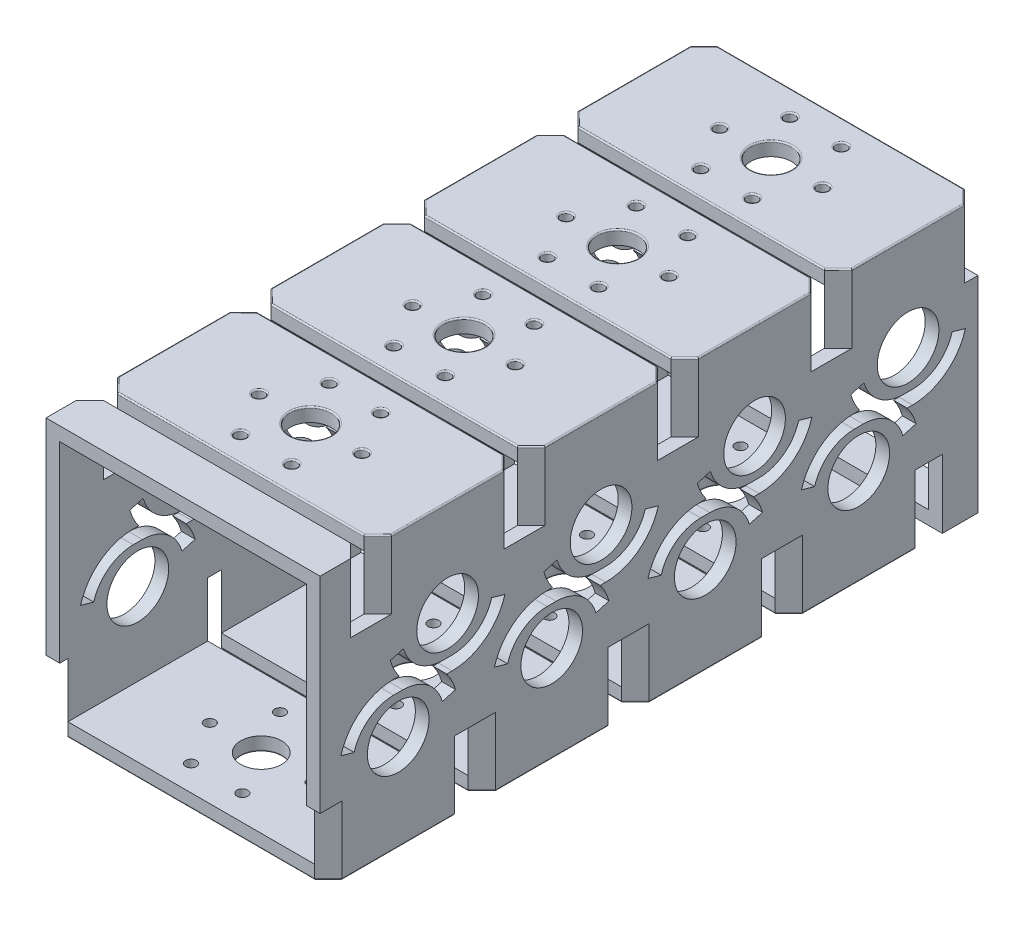
SolidWorks part; units mm, degrees
ref_plane "Front" through (0, 0, 0) normal (0, 0, 1) x (1, 0, 0)
ref_plane "Top" through (0, 0, 0) normal (0, 1, 0) x (1, 0, 0)
ref_plane "Right" through (0, 0, 0) normal (1, 0, 0) x (0, 0, -1)
sketch "Sketch1" plane through (0, 0, 0) normal (0, 0, 1) x (1, 0, 0)
  line L0 (6.35, 6.35) -> (120.65, 6.35)
  line L1 (0, 0) -> (127, 0)
  line L2 (0, 0) -> (0, 127)
  line L3 (0, 127) -> (127, 127)
  line L4 (127, 0) -> (127, 127)
  line L5 (120.65, 6.35) -> (120.65, 120.65)
  line L6 (6.35, 120.65) -> (120.65, 120.65)
  line L7 (6.35, 6.35) -> (6.35, 120.65)
  dimension "D1" = 127
  dimension "D2" = 6.35
extrude "Boss-Extrude1" add sketch "Sketch1" along normal blind 304.8
sketch "Sketch2" plane through (0, 127, 0) normal (0, 1, 0) x (1, 0, 0)
  line L0 (6.35, -64.77) -> (0, -64.77) construction
  line L1 (0, -304.8) -> (0, 0) construction
  line L2 (120.65, -71.12) -> (127, -71.12) construction
  line L3 (127, -304.8) -> (127, 0) construction
  line L5 (0, -64.77) -> (127, -64.77)
  line L6 (0, -64.77) -> (0, -71.12)
  line L7 (0, -71.12) -> (127, -71.12)
  line L8 (127, -64.77) -> (127, -71.12)
  line L9 (0, -64.77) -> (127, -71.12) construction
  line L10 (0, -71.12) -> (127, -64.77) construction
  point P13 (63.5, -67.945)
extrude "Cut-Extrude1" cut sketch "Sketch2" against normal blind 31.75
sketch "Sketch3" plane through (0, 127, 0) normal (0, 1, 0) x (1, 0, 0)
  line L0 (0, -58.42) -> (6.35, -64.77) construction
  line L1 (0, -58.42) -> (6.35, -64.77)
  line L2 (6.35, -64.77) -> (0, -64.77)
  line L4 (0, -64.77) -> (0, -58.42)
  line L5 (6.35, -71.12) -> (0, -77.47) construction
  line L6 (6.35, -71.12) -> (0, -77.47)
  line L7 (6.35, -71.12) -> (0, -71.12)
  line L8 (0, -71.12) -> (0, -77.47)
extrude "Cut-Extrude2" cut sketch "Sketch3" against normal blind 31.75
sketch "Sketch5" plane through (0, 0, 0) normal (-1, 0, 0) x (0, 0, 1)
  circle A0 centre (55.245, 44.45) radius 14.2875
  circle A1 centre (32.385, 82.55) radius 14.2875
  circle A2 centre (103.505, 82.55) radius 14.2875
  circle A3 centre (174.625, 82.55) radius 14.2875
  circle A4 centre (245.745, 82.55) radius 14.2875
  circle A9 centre (126.365, 44.45) radius 14.2875
  circle A10 centre (197.485, 44.45) radius 14.2875
  circle A11 centre (268.605, 44.45) radius 14.2875
  dimension "D1" = 28.575
  dimension "D4" = 4
  dimension "D2" = 4
  dimension "D3" = 1
extrude "Cut-Extrude4" cut sketch "Sketch5" against normal through all
pattern_linear "LPattern2" count 4 spacing 71.12 along (0, 0, 1) of "Cut-Extrude1"
pattern_linear "LPattern3" count 4 spacing 71.12 along (0, 0, 1) of "Cut-Extrude2"
sketch "Sketch6" plane through (0, 127, 0) normal (0, 1, 0) x (1, 0, 0)
  line L0 (6.35, 0) -> (0, -6.35) construction
  line L1 (6.35, 0) -> (0, -6.35)
  line L2 (6.35, 0) -> (0, 0)
  line L3 (0, 0) -> (0, -6.35)
  line L4 (127, -6.35) -> (120.65, 0) construction
  line L5 (127, -6.35) -> (120.65, 0)
  line L6 (127, -6.35) -> (127, 0)
  line L7 (127, 0) -> (120.65, 0)
extrude "Cut-Extrude5" cut sketch "Sketch6" against normal blind 31.75
sketch "Sketch7" plane through (0, 127, 0) normal (0, 1, 0) x (1, 0, 0)
  line L0 (127, -77.47) -> (120.65, -71.12) construction
  line L1 (127, -77.47) -> (120.65, -71.12)
  line L2 (120.65, -64.77) -> (127, -58.42) construction
  line L3 (120.65, -64.77) -> (127, -58.42)
  line L4 (120.65, -71.12) -> (127, -71.12)
  line L5 (127, -71.12) -> (127, -77.47)
  line L6 (120.65, -64.77) -> (127, -64.77)
  line L7 (127, -64.77) -> (127, -58.42)
extrude "Cut-Extrude6" cut sketch "Sketch7" against normal blind 31.75
pattern_linear "LPattern4" count 4 spacing 71.12 along (0, 0, 1) of "Cut-Extrude6"
sketch "Sketch8" plane through (0, 127, 0) normal (0, 1, 0) x (1, 0, 0)
  circle A1 centre (87.3125, -32.385) radius 2.4892
  circle A3 centre (75.4062, -53.0072) radius 2.4892
  circle A4 centre (51.5937, -53.0072) radius 2.4892
  circle A5 centre (39.6875, -32.385) radius 2.4892
  circle A6 centre (51.5938, -11.7628) radius 2.4892
  circle A7 centre (75.4063, -11.7628) radius 2.4892
  circle A9 centre (63.5, -32.385) radius 9.4869
  point P18 (63.5, -32.385)
  dimension "D1" = 18.9738
  dimension "D2" = 4.9784
  dimension "D3" = 6
extrude "Cut-Extrude7" cut sketch "Sketch8" against normal up to next (6.35 mm away)
pattern_linear "LPattern5" count 4 spacing 71.12 along (0, 0, 1) of "Cut-Extrude7"
ref_plane "Plane1" through (0, 63.5, 0) normal (0, 1, 0) x (1, 0, 0)
sketch "Sketch9" plane through (0, 0, 0) normal (0, -1, 0) x (1, 0, 0)
  circle A0 centre (51.5937, 34.6228) radius 2.4892
  circle A1 centre (39.6875, 55.245) radius 2.4892
  circle A2 centre (51.5937, 75.8672) radius 2.4892
  circle A3 centre (75.4062, 75.8672) radius 2.4892
  circle A4 centre (87.3125, 55.245) radius 2.4892
  circle A5 centre (75.4062, 34.6228) radius 2.4892
  circle A6 centre (63.5, 55.245) radius 9.4869
  circle A7 centre (51.5937, 105.7428) radius 2.4892
  circle A8 centre (39.6875, 126.365) radius 2.4892
  circle A9 centre (51.5937, 146.9872) radius 2.4892
  circle A10 centre (75.4062, 146.9872) radius 2.4892
  circle A11 centre (87.3125, 126.365) radius 2.4892
  circle A12 centre (75.4062, 105.7428) radius 2.4892
  circle A13 centre (63.5, 126.365) radius 9.4869
  circle A14 centre (51.5937, 176.8628) radius 2.4892
  circle A15 centre (39.6875, 197.485) radius 2.4892
  circle A16 centre (51.5937, 218.1072) radius 2.4892
  circle A17 centre (75.4062, 218.1072) radius 2.4892
  circle A18 centre (87.3125, 197.485) radius 2.4892
  circle A19 centre (75.4062, 176.8628) radius 2.4892
  circle A20 centre (63.5, 197.485) radius 9.4869
  circle A21 centre (51.5937, 247.9828) radius 2.4892
  circle A22 centre (39.6875, 268.605) radius 2.4892
  circle A23 centre (51.5937, 289.2272) radius 2.4892
  circle A24 centre (75.4062, 289.2272) radius 2.4892
  circle A25 centre (87.3125, 268.605) radius 2.4892
  circle A26 centre (75.4062, 247.9828) radius 2.4892
  circle A27 centre (63.5, 268.605) radius 9.4869
  dimension "D1" = 4.9784
  dimension "D2" = 18.9738
  dimension "D3" = 4
extrude "Cut-Extrude8" cut sketch "Sketch9" against normal up to next (6.35 mm away)
sketch "Sketch10" plane through (0, 0, 0) normal (0, -1, 0) x (1, 0, 0)
  line L0 (127, 304.8) -> (127, 0) construction
  line L1 (127, 22.86) -> (0, 22.86)
  line L2 (127, 22.86) -> (127, 16.51)
  line L3 (127, 16.51) -> (0, 16.51)
  line L4 (0, 22.86) -> (0, 16.51)
  line L5 (127, 22.86) -> (0, 16.51) construction
  line L6 (127, 16.51) -> (0, 22.86) construction
  line L7 (0, 304.8) -> (0, 0) construction
  line L8 (6.35, 22.86) -> (120.65, 22.86) construction
  line L9 (127, 93.98) -> (0, 93.98)
  line L10 (127, 93.98) -> (127, 87.63)
  line L11 (127, 87.63) -> (0, 87.63)
  line L12 (0, 93.98) -> (0, 87.63)
  line L13 (127, 93.98) -> (0, 87.63) construction
  line L14 (127, 87.63) -> (0, 93.98) construction
  line L15 (127, 165.1) -> (0, 165.1)
  line L16 (127, 165.1) -> (127, 158.75)
  line L17 (127, 158.75) -> (0, 158.75)
  line L18 (0, 165.1) -> (0, 158.75)
  line L19 (127, 165.1) -> (0, 158.75) construction
  line L20 (127, 158.75) -> (0, 165.1) construction
  line L21 (127, 236.22) -> (0, 236.22)
  line L22 (127, 236.22) -> (127, 229.87)
  line L23 (127, 229.87) -> (0, 229.87)
  line L24 (0, 236.22) -> (0, 229.87)
  line L25 (127, 236.22) -> (0, 229.87) construction
  line L26 (127, 229.87) -> (0, 236.22) construction
  line L27 (127, 307.34) -> (0, 307.34)
  line L28 (127, 307.34) -> (127, 300.99)
  line L29 (127, 300.99) -> (0, 300.99)
  line L30 (0, 307.34) -> (0, 300.99)
  line L31 (127, 307.34) -> (0, 300.99) construction
  line L32 (127, 300.99) -> (0, 307.34) construction
  point P4 (63.5, 19.685)
  point P16 (63.5, 90.805)
  point P21 (63.5, 161.925)
  point P26 (63.5, 233.045)
  point P31 (63.5, 304.165)
  dimension "D1" = 6.35
  dimension "D2" = 5
extrude "Cut-Extrude9" cut sketch "Sketch10" against normal blind 31.75
sketch "Sketch11" plane through (0, 0, 0) normal (0, -1, 0) x (1, 0, 0)
  line L0 (120.65, 22.86) -> (127, 29.21) construction
  line L1 (127, 81.28) -> (120.65, 87.63) construction
  line L2 (6.35, 87.63) -> (0, 81.28) construction
  line L3 (0, 29.21) -> (6.35, 22.86) construction
  line L4 (120.65, 22.86) -> (127, 29.21)
  line L5 (127, 81.28) -> (120.65, 87.63)
  line L6 (6.35, 87.63) -> (0, 81.28)
  line L7 (0, 29.21) -> (6.35, 22.86)
  line L8 (6.35, 22.86) -> (0, 22.86)
  line L9 (0, 22.86) -> (0, 29.21)
  line L10 (0, 81.28) -> (0, 87.63)
  line L11 (0, 87.63) -> (6.35, 87.63)
  line L12 (120.65, 22.86) -> (127, 22.86)
  line L13 (127, 22.86) -> (127, 29.21)
  line L14 (127, 81.28) -> (127, 87.63)
  line L15 (127, 87.63) -> (120.65, 87.63)
  line L16 (120.65, 93.98) -> (127, 100.33)
  line L17 (127, 152.4) -> (120.65, 158.75)
  line L18 (6.35, 158.75) -> (0, 152.4)
  line L19 (0, 100.33) -> (6.35, 93.98)
  line L20 (6.35, 93.98) -> (0, 93.98)
  line L21 (0, 93.98) -> (0, 100.33)
  line L22 (0, 152.4) -> (0, 158.75)
  line L23 (0, 158.75) -> (6.35, 158.75)
  line L24 (120.65, 93.98) -> (127, 93.98)
  line L25 (127, 93.98) -> (127, 100.33)
  line L26 (127, 152.4) -> (127, 158.75)
  line L27 (127, 158.75) -> (120.65, 158.75)
  line L28 (120.65, 165.1) -> (127, 171.45)
  line L29 (127, 223.52) -> (120.65, 229.87)
  line L30 (6.35, 229.87) -> (0, 223.52)
  line L31 (0, 171.45) -> (6.35, 165.1)
  line L32 (6.35, 165.1) -> (0, 165.1)
  line L33 (0, 165.1) -> (0, 171.45)
  line L34 (0, 223.52) -> (0, 229.87)
  line L35 (0, 229.87) -> (6.35, 229.87)
  line L36 (120.65, 165.1) -> (127, 165.1)
  line L37 (127, 165.1) -> (127, 171.45)
  line L38 (127, 223.52) -> (127, 229.87)
  line L39 (127, 229.87) -> (120.65, 229.87)
  line L40 (120.65, 236.22) -> (127, 242.57)
  line L41 (127, 294.64) -> (120.65, 300.99)
  line L42 (6.35, 300.99) -> (0, 294.64)
  line L43 (0, 242.57) -> (6.35, 236.22)
  line L44 (6.35, 236.22) -> (0, 236.22)
  line L45 (0, 236.22) -> (0, 242.57)
  line L46 (0, 294.64) -> (0, 300.99)
  line L47 (0, 300.99) -> (6.35, 300.99)
  line L48 (120.65, 236.22) -> (127, 236.22)
  line L49 (127, 236.22) -> (127, 242.57)
  line L50 (127, 294.64) -> (127, 300.99)
  line L51 (127, 300.99) -> (120.65, 300.99)
  dimension "D1" = 4
extrude "Cut-Extrude10" cut sketch "Sketch11" against normal blind 31.75
sketch "Sketch12" plane through (127, 0, 0) normal (1, 0, 0) x (0, 0, -1)
  line L0 (-53.1269, 62.23) -> (-57.3631, 62.23) construction
  line L1 (-53.1269, 62.23) -> (-57.3631, 62.23)
  line L3 (-34.802, 48.3859) -> (-28.6937, 50.1212)
  line L4 (-53.1269, 68.58) -> (-57.3631, 68.58)
  line L5 (-53.1269, 68.58) -> (-57.3631, 68.58)
  line L6 (-75.688, 48.3859) -> (-81.7963, 50.1212)
  line L7 (-146.808, 48.3859) -> (-152.9163, 50.1212)
  line L8 (-124.2469, 68.58) -> (-128.4831, 68.58)
  line L9 (-124.2469, 62.23) -> (-128.4831, 62.23)
  line L10 (-105.922, 48.3859) -> (-99.8137, 50.1212)
  line L11 (-217.928, 48.3859) -> (-224.0363, 50.1212)
  line L12 (-195.3669, 68.58) -> (-199.6031, 68.58)
  line L13 (-195.3669, 62.23) -> (-199.6031, 62.23)
  line L14 (-177.042, 48.3859) -> (-170.9337, 50.1212)
  line L15 (-289.048, 48.3859) -> (-295.1563, 50.1212)
  line L16 (-266.4869, 68.58) -> (-270.7231, 68.58)
  line L17 (-266.4869, 62.23) -> (-270.7231, 62.23)
  line L18 (-248.162, 48.3859) -> (-242.0537, 50.1212)
  arc A0 (-57.3631, 62.23) -> (-75.688, 48.3859) centre (-57.3631, 43.18) ccw construction
  arc A1 (-34.802, 48.3859) -> (-53.1269, 62.23) centre (-53.1269, 43.18) ccw construction
  arc A2 (-57.3631, 62.23) -> (-75.688, 48.3859) centre (-57.3631, 43.18) ccw
  arc A3 (-34.802, 48.3859) -> (-53.1269, 62.23) centre (-53.1269, 43.18) ccw
  arc A6 (-128.4831, 62.23) -> (-146.808, 48.3859) centre (-128.4831, 43.18) ccw
  arc A7 (-128.4831, 68.58) -> (-152.9163, 50.1212) centre (-128.4831, 43.18) ccw
  arc A8 (-28.6937, 50.1212) -> (-53.1269, 68.58) centre (-53.1269, 43.18) ccw
  arc A9 (-57.3631, 68.58) -> (-81.7963, 50.1212) centre (-57.3631, 43.18) ccw
  arc A10 (-28.6937, 50.1212) -> (-53.1269, 68.58) centre (-53.1269, 43.18) ccw
  arc A11 (-57.3631, 68.58) -> (-81.7963, 50.1212) centre (-57.3631, 43.18) ccw
  arc A12 (-99.8137, 50.1212) -> (-124.2469, 68.58) centre (-124.2469, 43.18) ccw
  arc A13 (-105.922, 48.3859) -> (-124.2469, 62.23) centre (-124.2469, 43.18) ccw
  arc A14 (-199.6031, 62.23) -> (-217.928, 48.3859) centre (-199.6031, 43.18) ccw
  arc A15 (-199.6031, 68.58) -> (-224.0363, 50.1212) centre (-199.6031, 43.18) ccw
  arc A16 (-170.9337, 50.1212) -> (-195.3669, 68.58) centre (-195.3669, 43.18) ccw
  arc A17 (-177.042, 48.3859) -> (-195.3669, 62.23) centre (-195.3669, 43.18) ccw
  arc A18 (-270.7231, 62.23) -> (-289.048, 48.3859) centre (-270.7231, 43.18) ccw
  arc A19 (-270.7231, 68.58) -> (-295.1563, 50.1212) centre (-270.7231, 43.18) ccw
  arc A20 (-242.0537, 50.1212) -> (-266.4869, 68.58) centre (-266.4869, 43.18) ccw
  arc A21 (-248.162, 48.3859) -> (-266.4869, 62.23) centre (-266.4869, 43.18) ccw
  dimension "D2" = 4
  dimension "D1" = 6.35
extrude "Cut-Extrude11" cut sketch "Sketch12" against normal through all
sketch "Sketch13" plane through (127, 0, 0) normal (1, 0, 0) x (0, 0, -1)
  line L0 (-34.5031, 64.77) -> (-30.2669, 64.77) construction
  line L1 (-34.5031, 64.77) -> (-30.2669, 64.77)
  line L3 (-52.828, 78.6141) -> (-58.9363, 76.8788)
  line L4 (-34.5031, 58.42) -> (-30.2669, 58.42)
  line L5 (-34.5031, 58.42) -> (-30.2669, 58.42)
  line L6 (-11.942, 78.6141) -> (-5.8337, 76.8788)
  line L7 (-123.948, 78.6141) -> (-130.0563, 76.8788)
  line L8 (-105.6231, 64.77) -> (-101.3869, 64.77)
  line L9 (-105.6231, 58.42) -> (-101.3869, 58.42)
  line L10 (-83.062, 78.6141) -> (-76.9537, 76.8788)
  line L11 (-195.068, 78.6141) -> (-201.1763, 76.8788)
  line L12 (-176.7431, 64.77) -> (-172.5069, 64.77)
  line L13 (-176.7431, 58.42) -> (-172.5069, 58.42)
  line L14 (-154.182, 78.6141) -> (-148.0737, 76.8788)
  line L15 (-266.188, 78.6141) -> (-272.2963, 76.8788)
  line L16 (-247.8631, 64.77) -> (-243.6269, 64.77)
  line L17 (-247.8631, 58.42) -> (-243.6269, 58.42)
  line L18 (-225.302, 78.6141) -> (-219.1937, 76.8788)
  arc A0 (-52.828, 78.6141) -> (-34.5031, 64.77) centre (-34.5031, 83.82) ccw construction
  arc A1 (-30.2669, 64.77) -> (-11.942, 78.6141) centre (-30.2669, 83.82) ccw construction
  arc A2 (-52.828, 78.6141) -> (-34.5031, 64.77) centre (-34.5031, 83.82) ccw
  arc A3 (-30.2669, 64.77) -> (-11.942, 78.6141) centre (-30.2669, 83.82) ccw
  arc A6 (-130.0563, 76.8788) -> (-105.6231, 58.42) centre (-105.6231, 83.82) ccw
  arc A7 (-123.948, 78.6141) -> (-105.6231, 64.77) centre (-105.6231, 83.82) ccw
  arc A8 (-30.2669, 58.42) -> (-5.8337, 76.8788) centre (-30.2669, 83.82) ccw
  arc A9 (-58.9363, 76.8788) -> (-34.5031, 58.42) centre (-34.5031, 83.82) ccw
  arc A10 (-30.2669, 58.42) -> (-5.8337, 76.8788) centre (-30.2669, 83.82) ccw
  arc A11 (-58.9363, 76.8788) -> (-34.5031, 58.42) centre (-34.5031, 83.82) ccw
  arc A12 (-101.3869, 58.42) -> (-76.9537, 76.8788) centre (-101.3869, 83.82) ccw
  arc A13 (-101.3869, 64.77) -> (-83.062, 78.6141) centre (-101.3869, 83.82) ccw
  arc A14 (-201.1763, 76.8788) -> (-176.7431, 58.42) centre (-176.7431, 83.82) ccw
  arc A15 (-195.068, 78.6141) -> (-176.7431, 64.77) centre (-176.7431, 83.82) ccw
  arc A16 (-172.5069, 58.42) -> (-148.0737, 76.8788) centre (-172.5069, 83.82) ccw
  arc A17 (-172.5069, 64.77) -> (-154.182, 78.6141) centre (-172.5069, 83.82) ccw
  arc A18 (-272.2963, 76.8788) -> (-247.8631, 58.42) centre (-247.8631, 83.82) ccw
  arc A19 (-266.188, 78.6141) -> (-247.8631, 64.77) centre (-247.8631, 83.82) ccw
  arc A20 (-243.6269, 58.42) -> (-219.1937, 76.8788) centre (-243.6269, 83.82) ccw
  arc A21 (-243.6269, 64.77) -> (-225.302, 78.6141) centre (-243.6269, 83.82) ccw
  dimension "D2" = 4
  dimension "D1" = 6.35
extrude "Cut-Extrude12" cut sketch "Sketch13" against normal through all
fillet "Fillet1" radius 0.635 120 edges at (123.825, 127, 274.955) (63.5, 127, 278.13) (3.175, 127, 274.955) (0, 127, 245.745) (3.175, 127, 216.535) (63.5, 127, 213.36) (123.825, 127, 216.535) (127, 127, 245.745) (75.4063, 127, 227.612) (51.5938, 127, 227.612) (39.6875, 127, 248.2342) (51.5937, 127, 268.8564) (87.3125, 127, 248.2342) (63.5, 127, 255.2319) (75.4062, 127, 268.8564) (3.175, 127, 203.835) (0, 127, 174.625) (3.175, 127, 145.415) (63.5, 127, 142.24) (123.825, 127, 145.415) (127, 127, 174.625) (123.825, 127, 203.835) (63.5, 127, 207.01) (63.5, 127, 184.1119) (87.3125, 127, 177.1142) (75.4063, 127, 156.492) (51.5938, 127, 156.492) (39.6875, 127, 177.1142) (51.5937, 127, 197.7364) (75.4062, 127, 197.7364) (3.175, 127, 132.715) (0, 127, 103.505) (3.175, 127, 74.295) (63.5, 127, 71.12) (123.825, 127, 74.295) (127, 127, 103.505) (123.825, 127, 132.715) (63.5, 127, 135.89) (87.3125, 127, 105.9942) (75.4063, 127, 85.372) (51.5938, 127, 85.372) (63.5, 127, 112.9919) (75.4062, 127, 126.6164) (51.5937, 127, 126.6164) (39.6875, 127, 105.9942) (3.175, 127, 61.595) (0, 127, 32.385) (3.175, 127, 3.175) (63.5, 127, 0) (123.825, 127, 3.175) (127, 127, 32.385) (123.825, 127, 61.595) (63.5, 127, 64.77) (75.4063, 127, 14.252) (51.5938, 127, 14.252) (63.5, 127, 41.8719) (75.4062, 127, 55.4964) (51.5937, 127, 55.4964) (39.6875, 127, 34.8742) (87.3125, 127, 34.8742) (123.825, 0, 26.035) (63.5, 0, 22.86) (3.175, 0, 26.035) (0, 0, 55.245) (3.175, 0, 84.455) (63.5, 0, 87.63) (123.825, 0, 84.455) (127, 0, 55.245) (39.6875, 0, 52.7558) (51.5937, 0, 73.378) (75.4062, 0, 73.378) (87.3125, 0, 52.7558) (75.4062, 0, 32.1336) (63.5, 0, 45.7581) (51.5937, 0, 32.1336) (123.825, 0, 97.155) (63.5, 0, 93.98) (3.175, 0, 97.155) (0, 0, 126.365) (3.175, 0, 155.575) (63.5, 0, 158.75) (123.825, 0, 155.575) (127, 0, 126.365) (39.6875, 0, 123.8758) (51.5937, 0, 103.2536) (63.5, 0, 116.8781) (75.4062, 0, 103.2536) (87.3125, 0, 123.8758) (75.4062, 0, 144.498) (51.5937, 0, 144.498) (3.175, 0, 168.275) (0, 0, 197.485) (3.175, 0, 226.695) (63.5, 0, 229.87) (123.825, 0, 226.695) (127, 0, 197.485) (123.825, 0, 168.275) (63.5, 0, 165.1) (51.5937, 0, 174.3736) (39.6875, 0, 194.9958) (51.5937, 0, 215.618) (75.4062, 0, 215.618) (87.3125, 0, 194.9958) (75.4062, 0, 174.3736) (63.5, 0, 187.9981) (3.175, 0, 297.815) (63.5, 0, 300.99) (123.825, 0, 297.815) (127, 0, 268.605) (123.825, 0, 239.395) (63.5, 0, 236.22) (3.175, 0, 239.395) (0, 0, 268.605) (51.5937, 0, 245.4936) (39.6875, 0, 266.1158) (51.5937, 0, 286.738) (75.4062, 0, 286.738) (63.5, 0, 259.1181) (75.4062, 0, 245.4936) (87.3125, 0, 266.1158)
